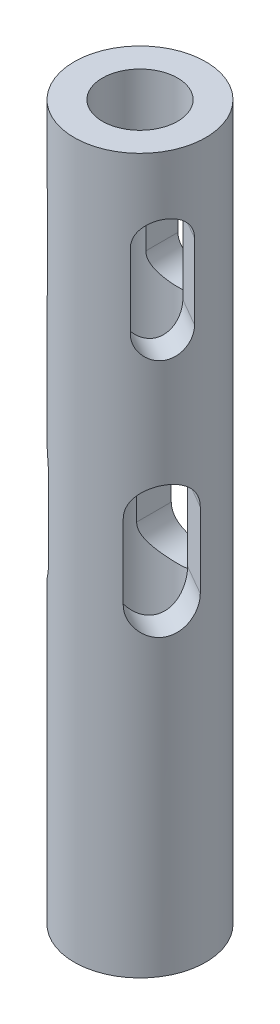
SolidWorks part; units mm, degrees
ref_plane "Front Plane" through (0, 0, 0) normal (0, 0, 1) x (1, 0, 0)
ref_plane "Top Plane" through (0, 0, 0) normal (0, 1, 0) x (1, 0, 0)
ref_plane "Right Plane" through (0, 0, 0) normal (1, 0, 0) x (0, 0, -1)
sketch "Sketch1" plane through (0, 0, 0) normal (0, 0, 1) x (1, 0, 0)
  line L0 (-0.5, 38) -> (-0.5, -38)
  line L1 (-3.5, 38) -> (3.5, 38)
  line L2 (-3.5, 38) -> (-3.5, -38)
  line L3 (-3.5, -38) -> (3.5, -38)
  line L4 (3.5, 38) -> (3.5, -38)
  line L5 (-3.5, 38) -> (3.5, -38) construction
  line L6 (-3.5, -38) -> (3.5, 38) construction
  line L7 (3.5, -38) -> (3.5, -41.6056) construction
  line L8 (3.5, -38.9692) -> (3.5, -38)
  line L9 (-3.5, -23.3291) -> (-3.5, -38)
  point P0 (0, 0)
  dimension "D2" = 3
  dimension "D1" = 7
  dimension "D3" = 76
revolve "Revolve1" add sketch "Sketch1" angle 360 about L4
sketch "Sketch2" plane through (0, 0, 0) normal (0, 0, 1) x (1, 0, 0)
  line L0 (0, 0) -> (0, 60.7198) construction
sketch "Sketch3" plane through (0, 0, 0) normal (0, 0, 1) x (1, 0, 0)
  line L0 (3.5, 38) -> (3.5, -38) construction
  line L1 (7.5, 38) -> (-0.5, 38) construction
  line L2 (-3.5, -38) -> (10.5, -38) construction
  line L3 (3.5, 21.2513) -> (3.5, 29.2513) construction
  line L4 (1, 21.2513) -> (1, 29.2513)
  line L5 (6, 21.2513) -> (6, 29.2513)
  line L6 (10.5, 38) -> (-3.5, 38) construction
  line L7 (3.5, 4.25) -> (3.5, -3.75) construction
  line L8 (6.5, 4.25) -> (6.5, -3.75)
  line L9 (0.5, 4.25) -> (0.5, -3.75)
  circle A0 centre (3.5, 25.2513) radius 12.5
  circle A1 centre (3.5, 0.25) radius 12.5
  arc A2 (1, 21.2513) -> (6, 21.2513) centre (3.5, 21.2513) ccw
  arc A3 (6, 29.2513) -> (1, 29.2513) centre (3.5, 29.2513) ccw
  arc A4 (6.5, 4.25) -> (0.5, 4.25) centre (3.5, 4.25) ccw
  arc A5 (0.5, -3.75) -> (6.5, -3.75) centre (3.5, -3.75) ccw
  point P12 (3.5, 25.2513)
  point P21 (3.5, 0.25)
  dimension "D1" = 25
  dimension "D3" = 2.5
  dimension "D6" = 3
  dimension "D2" = 8
  dimension "D4" = 12.7487
  dimension "D5" = 8
  dimension "D7" = 37.75
extrude "Cut-Extrude1" cut sketch "Sketch3" against normal blind 10 contours L4 A3 L5 A2 | L9 A5 L8 A4
sketch "Sketch4" plane through (0, 0, 0) normal (0, 0, 1) x (1, 0, 0)
  line L0 (3.5, 38) -> (3.5, -49962) construction
  line L1 (7.5, 38) -> (-0.5, 38) construction
  point P4 (3.5, 38)
pattern_circular "CirPattern1" count 3 over 360 about axis through (3.5, 0, 0) along (0, 1, 0) of "Cut-Extrude1"
